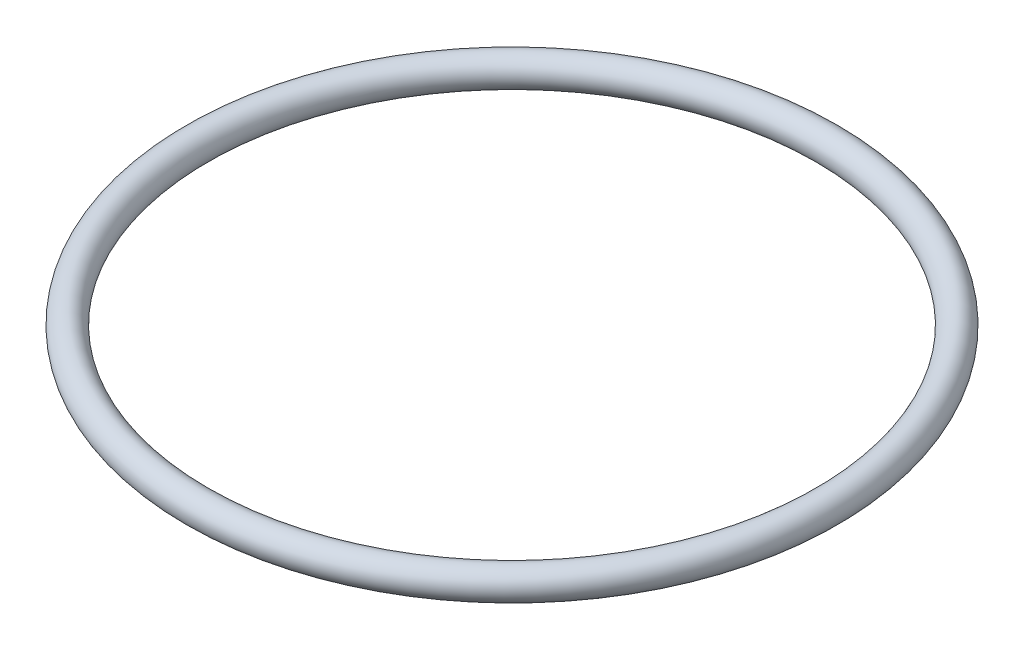
SolidWorks part; units mm, degrees
material "BUTYL"
ref_plane "Front Plane" through (0, 0, 0) normal (0, 0, 1) x (1, 0, 0)
ref_plane "Top Plane" through (0, 0, 0) normal (0, 1, 0) x (1, 0, 0)
ref_plane "Right Plane" through (0, 0, 0) normal (1, 0, 0) x (0, 0, -1)
sketch "Sketch1" plane through (0, 0, 0) normal (0, 1, 0) x (1, 0, 0)
  circle A0 centre (0, 0) radius 23.8715
  dimension "D1" = 47.743
sketch "Sketch2" plane through (0, 0, 0) normal (0, 0, 1) x (1, 0, 0)
  line L0 (23.8715, 0) -> (-23.8715, 0) construction
  circle A1 centre (-23.8715, 0) radius 1.143
  dimension "D1" = 2.286
sweep "Sweep1" add profiles "Sketch2" path "Sketch1"
